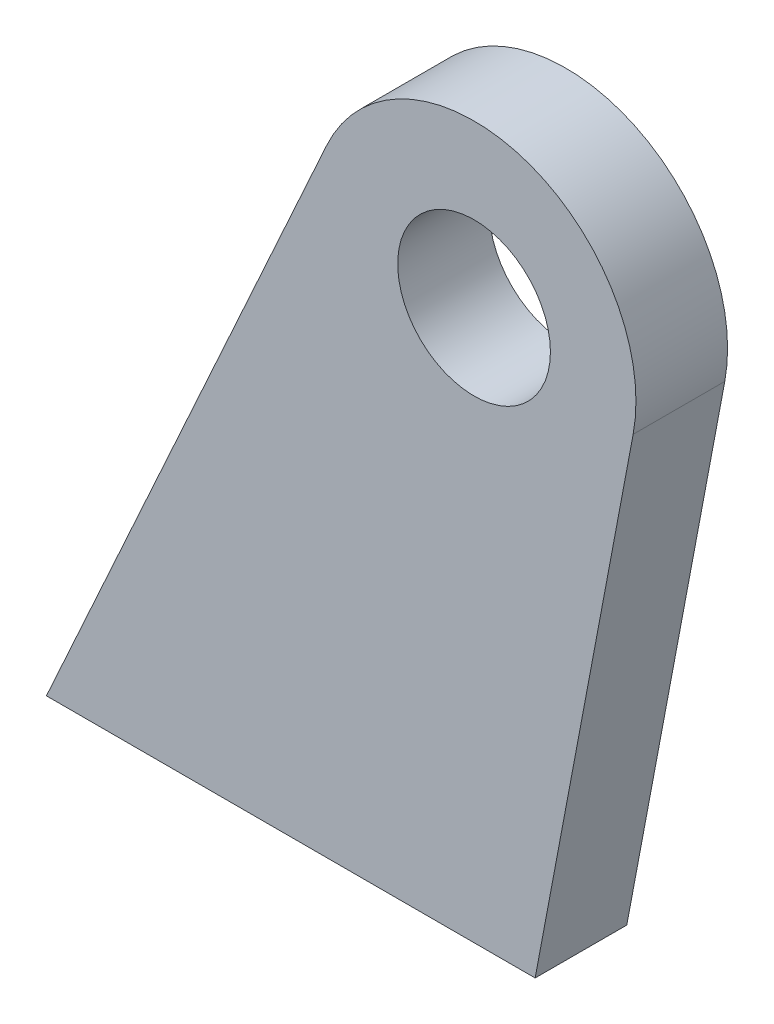
SolidWorks part; units mm, degrees
material "ASTM A36 Steel"
ref_plane "Front Plane" through (0, 0, 0) normal (0, 0, 1) x (1, 0, 0)
ref_plane "Top Plane" through (0, 0, 0) normal (0, 1, 0) x (1, 0, 0)
ref_plane "Right Plane" through (0, 0, 0) normal (1, 0, 0) x (0, 0, -1)
sketch "Sketch1" plane through (0, 0, 0) normal (0, 0, 1) x (1, 0, 0)
  line L0 (-30.6405, 13.9219) -> (-88.9, -114.3)
  line L1 (-88.9, -114.3) -> (12.7, -114.3)
  line L2 (33.0724, -6.2348) -> (12.7, -114.3)
  circle A0 centre (0, 0) radius 15.875
  arc A1 (33.0724, -6.2348) -> (-30.6405, 13.9219) centre (0, 0) ccw
  point P9 (-33.655, 0)
  point P10 (33.655, 0)
  dimension "D1" = 17.78
  dimension "D2" = 31.75
  dimension "D3" = 101.6
  dimension "D4" = 12.7
  dimension "D5" = 114.3
extrude "Boss-Extrude1" add sketch "Sketch1" along normal blind 19.05 contours L2 A1 L0 L1 A0
